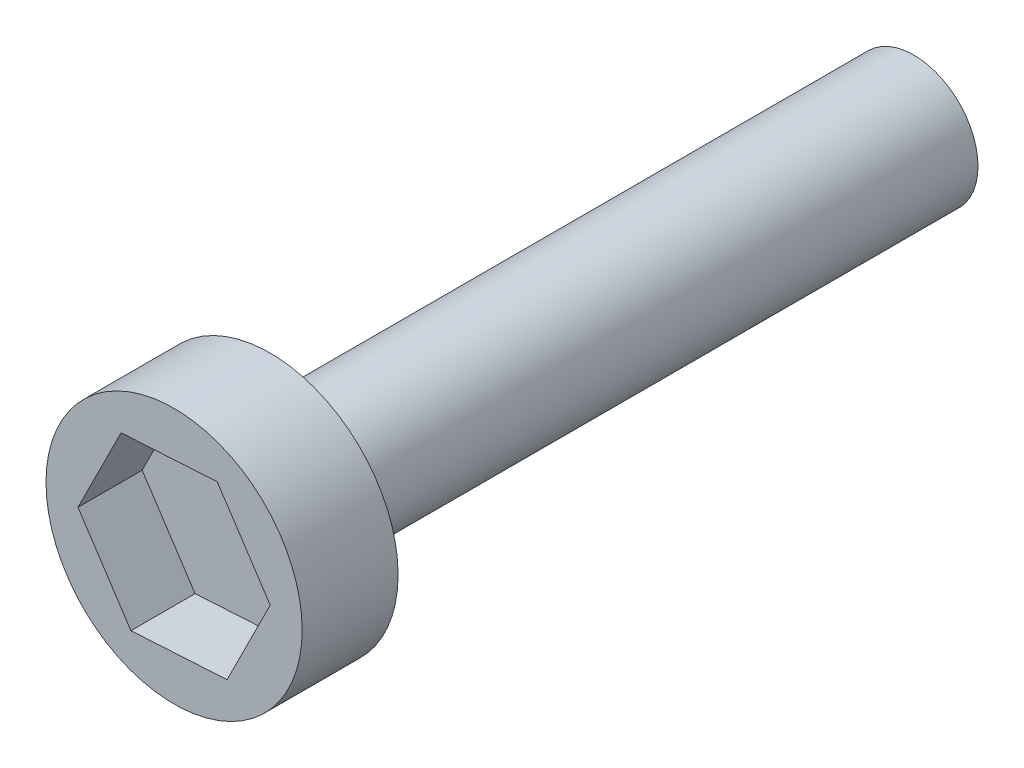
SolidWorks part; units mm, degrees
ref_plane "Front Plane" through (0, 0, 0) normal (0, 0, 1) x (1, 0, 0)
ref_plane "Top Plane" through (0, 0, 0) normal (0, 1, 0) x (1, 0, 0)
ref_plane "Right Plane" through (0, 0, 0) normal (1, 0, 0) x (0, 0, -1)
sketch "Sketch1" plane through (0, 0, 0) normal (0, 0, 1) x (1, 0, 0)
  circle A0 centre (0, 0) radius 12.6998
extrude "Boss-Extrude1" add sketch "Sketch1" along normal blind 127
sketch "Sketch3" plane through (0, 0, 0) normal (1, 0, 0) x (0, 0, -1)
  line L0 (-127.3647, 0) -> (-146.3461, 0)
  line L1 (-146.3461, 0) -> (-146.3461, 25.3397)
  line L2 (-146.3461, 25.3397) -> (-127.3647, 25.3397)
  line L3 (-127.3647, 25.3397) -> (-127.3647, 0)
revolve "Revolve1" add sketch "Sketch3" angle 360 about L0
sketch "Sketch4" plane through (0, 0, 146.3461) normal (0, 0, 1) x (1, 0, 0)
  line L1 (8.5381, 17.0295) -> (-10.4789, 15.9089)
  line L2 (-10.4789, 15.9089) -> (-19.017, -1.1206)
  line L3 (-19.017, -1.1206) -> (-8.5381, -17.0295)
  line L4 (-8.5381, -17.0295) -> (10.4789, -15.9089)
  line L5 (10.4789, -15.9089) -> (19.017, 1.1206)
  line L6 (19.017, 1.1206) -> (8.5381, 17.0295)
  circle A0 centre (0, 0) radius 16.4978 construction
extrude "Cut-Extrude1" cut sketch "Sketch4" against normal blind 12.7
sketch3d "URDF Reference"
  line L0 (0, 0, 0) -> (10, 0, 0) construction
  line L1 (0, 0, 0) -> (0, 0, -10) construction
  point P0 (0, 0, 0)
